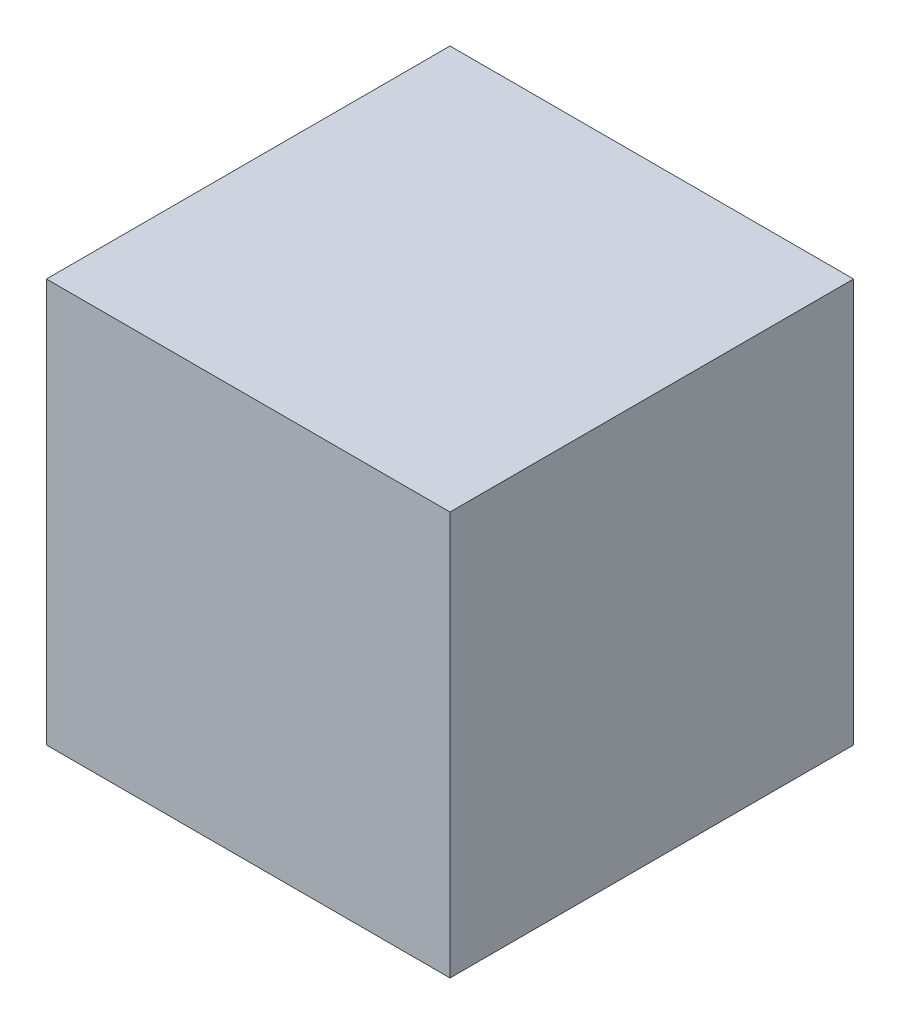
SolidWorks part; units mm, degrees
ref_plane "Front Plane" through (0, 0, 0) normal (0, 0, 1) x (1, 0, 0)
ref_plane "Top Plane" through (0, 0, 0) normal (0, 1, 0) x (1, 0, 0)
ref_plane "Right Plane" through (0, 0, 0) normal (1, 0, 0) x (0, 0, -1)
sketch "Sketch1" plane through (0, 0, 0) normal (0, 0, 1) x (1, 0, 0)
  line L1 (0, 0) -> (10, 0)
  line L2 (0, 0) -> (0, 10)
  line L3 (0, 10) -> (10, 10)
  line L4 (10, 0) -> (10, 10)
  dimension "D1" = 10
  dimension "D2" = 10
extrude "Boss-Extrude1" add sketch "Sketch1" along normal blind 10
